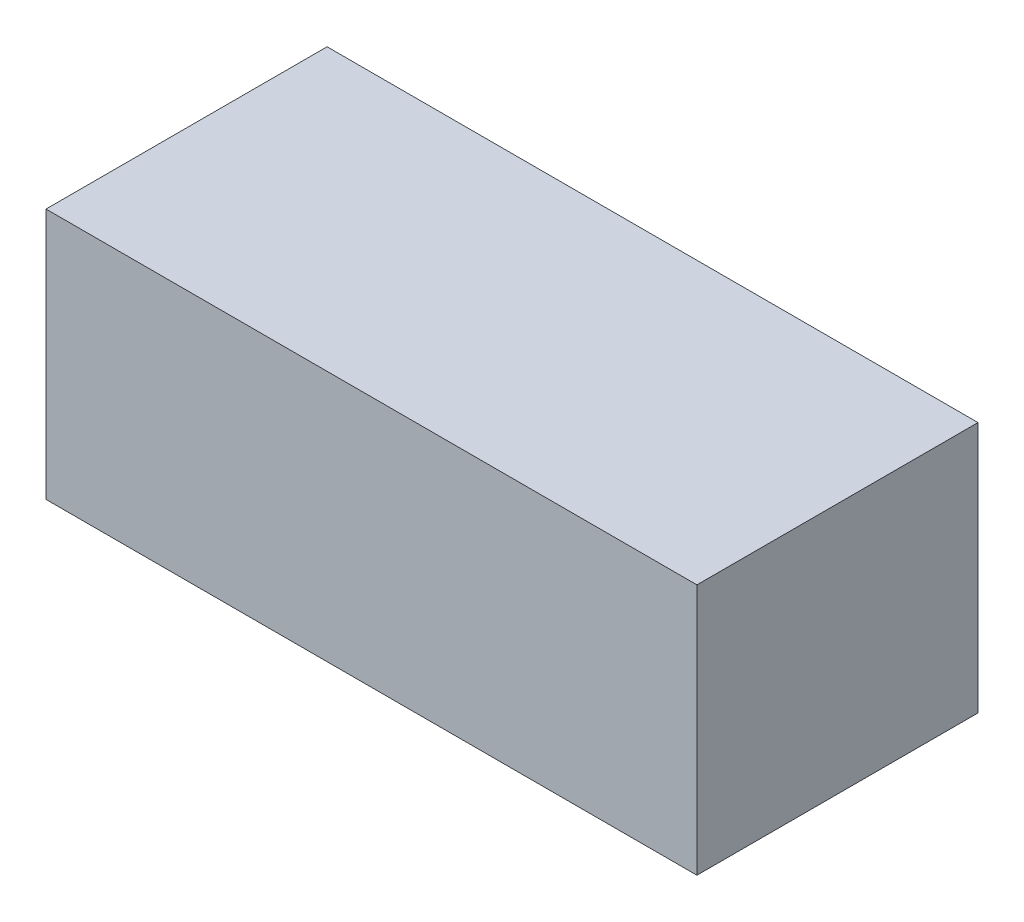
SolidWorks part; units mm, degrees
material "Silicon"
ref_plane "Front Plane" through (0, 0, 0) normal (0, 0, 1) x (1, 0, 0)
ref_plane "Top Plane" through (0, 0, 0) normal (0, 1, 0) x (1, 0, 0)
ref_plane "Right Plane" through (0, 0, 0) normal (1, 0, 0) x (0, 0, -1)
sketch "Sketch1" plane through (0, 0, 0) normal (0, 1, 0) x (1, 0, 0)
  line L1 (0, 0) -> (4.4, 0)
  line L2 (0, 0) -> (0, 1.9)
  line L3 (0, 1.9) -> (4.4, 1.9)
  line L4 (4.4, 0) -> (4.4, 1.9)
  dimension "D1" = 4.4
  dimension "D2" = 1.9
extrude "Boss-Extrude1" add sketch "Sketch1" along normal blind 1.7
